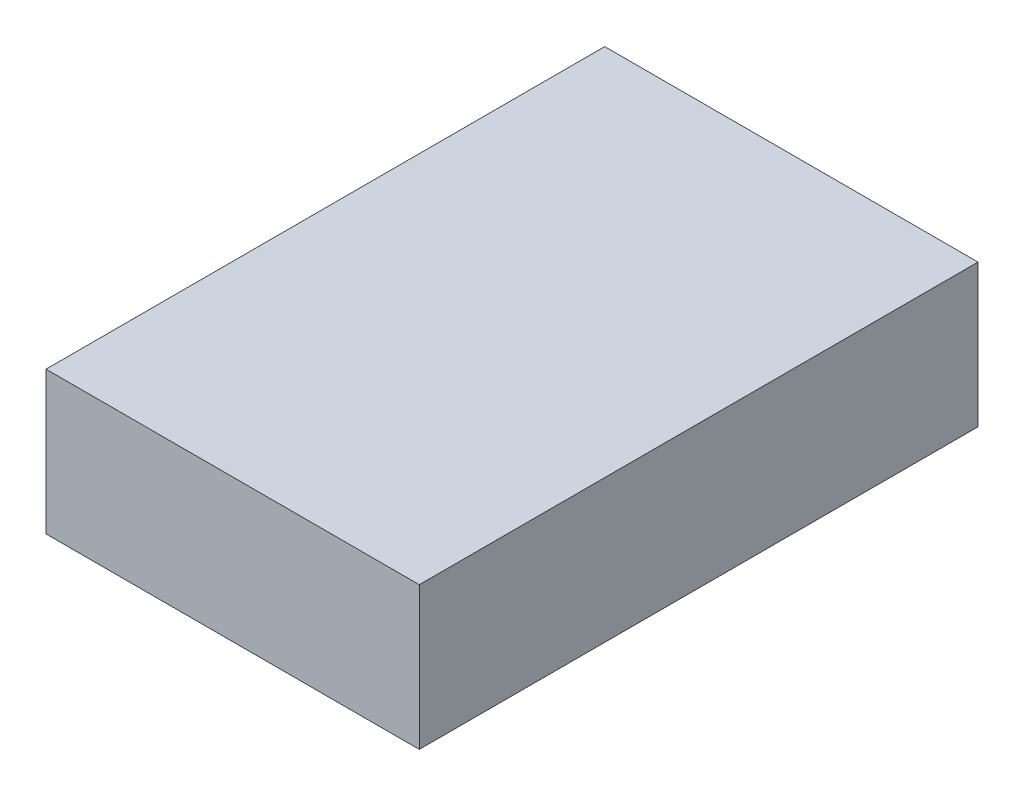
SolidWorks part; units mm, degrees
ref_plane "Front Plane" through (0, 0, 0) normal (0, 0, 1) x (1, 0, 0)
ref_plane "Top Plane" through (0, 0, 0) normal (0, 1, 0) x (1, 0, 0)
ref_plane "Right Plane" through (0, 0, 0) normal (1, 0, 0) x (0, 0, -1)
sketch "Sketch1" plane through (0, 0, 0) normal (0, 1, 0) x (1, 0, 0)
  line L1 (-19.939, -29.845) -> (19.939, -29.845)
  line L2 (-19.939, -29.845) -> (-19.939, 29.845)
  line L3 (-19.939, 29.845) -> (19.939, 29.845)
  line L4 (19.939, -29.845) -> (19.939, 29.845)
  line L5 (-19.939, -29.845) -> (19.939, 29.845) construction
  line L6 (-19.939, 29.845) -> (19.939, -29.845) construction
  point P0 (0, 0)
  dimension "D1" = 59.69
  dimension "D2" = 39.878
extrude "Boss-Extrude1" add sketch "Sketch1" along normal blind 15.24
